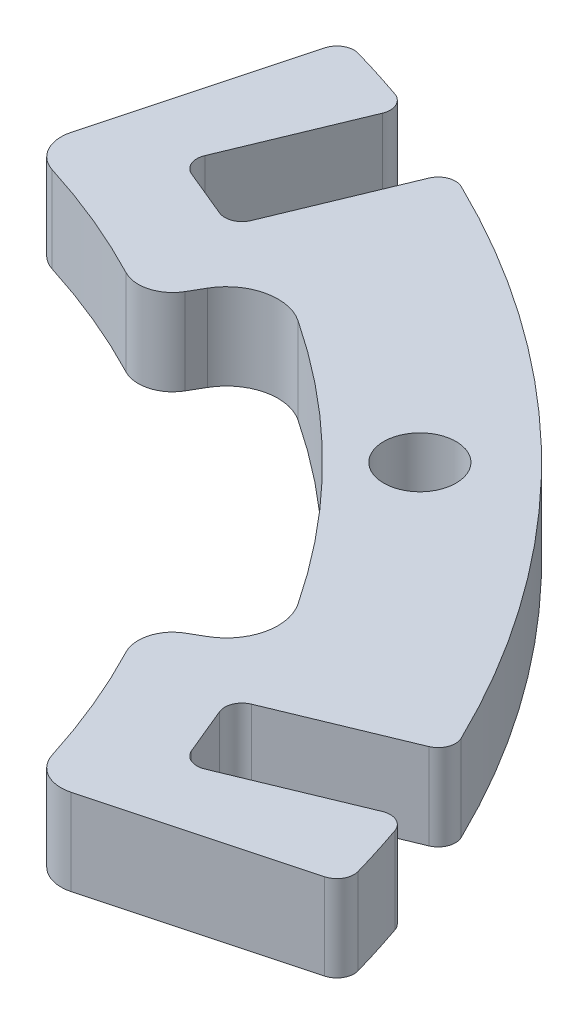
SolidWorks part; units mm, degrees
material "A-Glass Fiber"
ref_plane "Front Plane" through (0, 0, 0) normal (0, 0, 1) x (1, 0, 0)
ref_plane "Top Plane" through (0, 0, 0) normal (0, 1, 0) x (1, 0, 0)
ref_plane "Right Plane" through (0, 0, 0) normal (1, 0, 0) x (0, 0, -1)
sketch "Sketch1" plane through (0, 0, 0) normal (0, 1, 0) x (1, 0, 0)
  circle A0 centre (0, 0) radius 45
  circle A1 centre (0, 0) radius 60
  point P20 (53.9432, 10.73)
  point P27 (45.7308, -30.5564)
  point P34 (10.73, -53.9432)
  point P66 (30.5564, 45.7308)
  dimension "D1" = 90
  dimension "D2" = 120
extrude "Boss-Extrude1" add sketch "Sketch1" along normal blind 5
sketch "Sketch2" plane through (0, 5, 0) normal (0, 1, 0) x (1, 0, 0)
  line L0 (12.399, 46.2738) -> (12.1535, 45.3574)
  line L1 (-12.399, 46.2738) -> (-12.1535, 45.3574)
  line L2 (-13.486, 42.9317) -> (13.486, 42.9317)
  line L3 (0, 0) -> (0, 70.7151) construction
  arc A0 (12.1535, 45.3574) -> (13.486, 42.9317) centre (14.0853, 44.8398) ccw
  arc A1 (-12.1535, 45.3574) -> (-13.486, 42.9317) centre (-14.0853, 44.8398) cw
  circle A2 centre (0, 0) radius 51
  arc A3 (10.0951, 49.9909) -> (-10.0951, 49.9909) centre (0, 0) ccw
  arc A4 (-10.0951, 49.9909) -> (-12.399, 46.2738) centre (-9.5012, 47.0503) ccw
  arc A7 (10.0951, 49.9909) -> (12.399, 46.2738) centre (9.5012, 47.0503) cw
  circle A17 centre (0, 0) radius 45 construction
  arc A20 (-13.486, 42.9317) -> (13.486, 42.9317) centre (0, 0) ccw construction
  dimension "D4" = 2
  dimension "D5" = 3
  dimension "D2" = 30
  dimension "D1" = 9
extrude "Cut-Extrude1" cut sketch "Sketch2" against normal through all
pattern_circular "CirPattern1" count 8 over 360 about axis through (0, 0, 0) along (0, 1, 0) of "Cut-Extrude1"
sketch "Sketch3" plane through (0, 5, 0) normal (0, 1, 0) x (1, 0, 0)
  line L0 (0, 0) -> (38.8909, 38.8909) construction
  circle A0 centre (38.8909, 38.8909) radius 2.1
  dimension "D2" = 4.2
  dimension "D1" = 55
extrude "Cut-Extrude2" cut sketch "Sketch3" against normal through all
pattern_circular "CirPattern2" count 4 over 360 about axis through (0, 0, 0) along (0, 1, 0) of "Cut-Extrude2"
sketch "Skizze1" plane through (0, 5, 0) normal (0, 1, 0) x (1, 0, 0)
  line L0 (0, 0) -> (24.7981, 92.5476)
  line L1 (24.7981, 92.5476) -> (92.5476, 24.7981)
  line L2 (92.5476, 24.7981) -> (0, 0)
extrude "Schnitt-Linear austragen1" cut sketch "Skizze1" against normal through all flip side to cut
fillet "Verrundung1" radius 1 2 edges at (15.5291, 2.5, -57.9555) (57.9555, 2.5, -15.5291)
sketch "Skizze2" plane through (0, 5, 0) normal (0, 1, 0) x (1, 0, 0)
  line L0 (0, 0) -> (25.0325, 60.4339) construction
  line L1 (12.1535, 45.3574) -> (15.2681, 56.9814) construction
  line L2 (23.9531, 41.488) -> (23.4787, 40.6663) construction
  line L4 (16.8245, 47.1507) -> (21.4439, 45.2373)
  line L5 (16.8245, 47.1507) -> (20.6513, 56.3895)
  line L6 (20.6513, 56.3895) -> (25.2707, 54.4761)
  line L7 (21.4439, 45.2373) -> (25.2707, 54.4761)
  line L8 (16.8245, 47.1507) -> (25.2707, 54.4761) construction
  line L9 (20.6513, 56.3895) -> (21.4439, 45.2373) construction
  arc A0 (57.684, 16.5092) -> (16.5092, 57.684) centre (0, 0) ccw construction
  point P7 (21.0476, 50.8134)
  dimension "D2" = 10
  dimension "D1" = 5
extrude "Schnitt-Linear austragen2" cut sketch "Skizze2" against normal through all
fillet "Verrundung2" radius 1 4 edges at (25.2508, 2.5, -54.4279) (21.4439, 2.5, -45.2373) (16.8245, 2.5, -47.1507) (20.6314, 2.5, -56.3413)
pattern_circular "Kreismuster1" count 2 every 45 about axis through (0, 0, 0) along (0, 1, 0) of "Schnitt-Linear austragen2", "Verrundung2"
